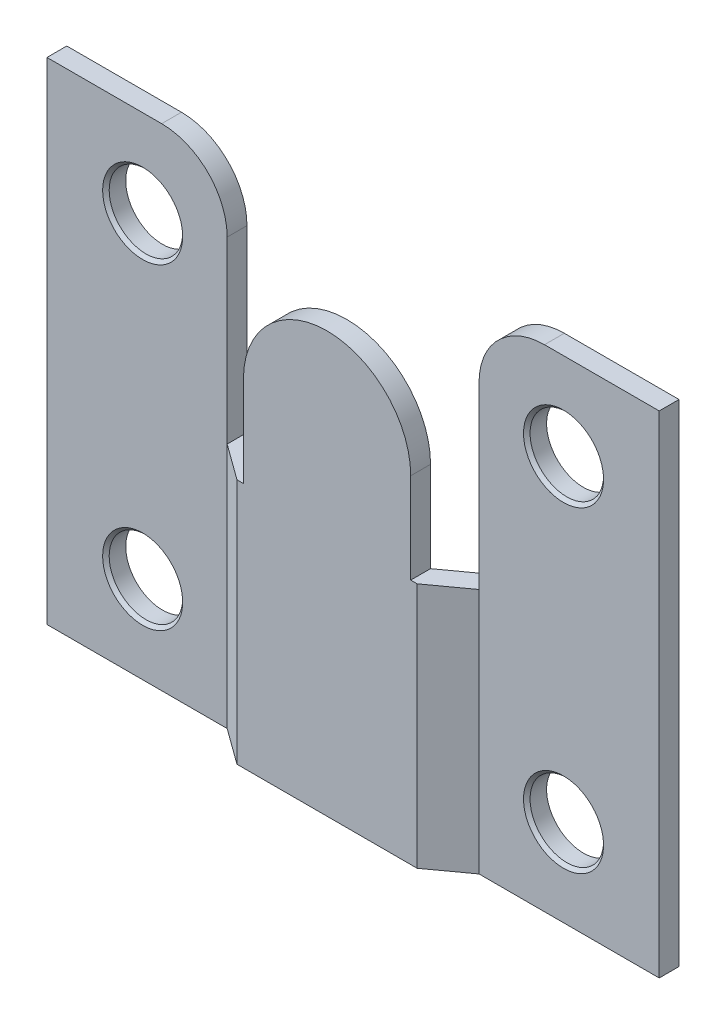
SolidWorks part; units mm, degrees
ref_plane "Front" through (0, 0, 0) normal (0, 0, 1) x (1, 0, 0)
ref_plane "Top" through (0, 0, 0) normal (0, 1, 0) x (1, 0, 0)
ref_plane "Right" through (0, 0, 0) normal (1, 0, 0) x (0, 0, -1)
sketch "Sketch1" plane through (0, 0, 0) normal (0, 1, 0) x (1, 0, 0)
  line L0 (9.7701, 2.0193) -> (6.9894, 0)
  line L1 (6.9894, 0) -> (-6.9894, 0)
  line L2 (-6.9894, 0) -> (-9.7701, 2.0193)
  line L3 (-9.7701, 2.0193) -> (-23.749, 2.0193)
  line L4 (9.7701, 2.0193) -> (23.749, 2.0193)
  line L5 (0, 0) -> (0, 3.556) construction
  line L6 (9.271, 3.556) -> (23.749, 3.556)
  line L7 (9.271, 3.556) -> (6.4903, 1.5367)
  line L8 (6.4903, 1.5367) -> (-6.4903, 1.5367)
  line L9 (-6.4903, 1.5367) -> (-9.271, 3.556)
  line L10 (-9.271, 3.556) -> (-23.749, 3.556)
  line L12 (-23.749, 3.556) -> (-23.749, 2.0193)
  line L13 (23.749, 3.556) -> (23.749, 2.0193)
  point P15 (0, 0)
  dimension "D1" = 47.498
  dimension "D2" = 3.556
  dimension "D3" = 14.478
  dimension "D4" = 1.5367
extrude "Boss-Extrude1" add sketch "Sketch1" along normal blind 38.1
sketch "Sketch2" plane through (0, 0, 0) normal (0, 0, 1) x (1, 0, 0)
  line L0 (-23.749, 19.05) -> (23.749, 19.05) construction
  line L1 (-23.749, 38.1) -> (-23.749, 0) construction
  line L2 (23.749, 38.1) -> (23.749, 0) construction
  line L3 (-9.7701, 38.1) -> (-9.7701, 0) construction
  line L4 (-9.7701, 19.05) -> (-6.9894, 19.05)
  line L5 (-9.7701, 19.05) -> (-9.7701, 38.1)
  line L6 (-9.7701, 38.1) -> (-6.9894, 38.1)
  line L7 (-6.9894, 19.05) -> (-6.9894, 38.1)
  line L8 (6.9894, 38.1) -> (6.9894, 0) construction
  line L9 (6.9894, 19.05) -> (9.7701, 19.05)
  line L10 (6.9894, 19.05) -> (6.9894, 38.1)
  line L11 (6.9894, 38.1) -> (9.7701, 38.1)
  line L12 (9.7701, 19.05) -> (9.7701, 38.1)
sketch "Sketch5" plane through (0, 0, -2.0193) normal (0, 0, 1) x (1, 0, 0)
  line L0 (-9.7701, 0) -> (-9.7701, 19.1135) construction
  line L1 (-9.7701, 38.1) -> (-9.7701, 0) construction
  dimension "D1" = 19.1135
sketch "Sketch3" plane through (0, 38.1, 0) normal (0, 1, 0) x (1, 0, 0)
  line L0 (-9.7701, 3.9185) -> (-9.7701, 2.0193)
  line L1 (-9.7701, 2.0193) -> (-6.4903, -0.3625)
  line L2 (-6.4903, 1.5367) -> (-6.4903, -0.3625)
  line L3 (-6.4903, 1.5367) -> (-9.271, 3.556) construction
  line L4 (-6.4903, 1.5367) -> (-9.7701, 3.9185)
  line L5 (0, 0) -> (0, 2.8575) construction
  line L6 (-6.9894, 0) -> (6.9894, 0) construction
  line L7 (-9.7701, 2.0193) -> (-6.9894, 0) construction
  line L8 (6.4903, 1.5367) -> (9.7701, 3.9185)
  line L9 (6.4903, 1.5367) -> (6.4903, -0.3625)
  line L10 (9.7701, 2.0193) -> (6.4903, -0.3625)
  line L11 (9.7701, 3.9185) -> (9.7701, 2.0193)
extrude "Cut-Extrude2" cut sketch "Sketch3" against normal up to vertex (18.9865 mm away) up to point (-9.7701, 19.1135, -2.0193)
sketch "Sketch6" plane through (0, 0, -1.5367) normal (0, 0, -1) x (-1, 0, 0)
  line L0 (-6.4903, 38.1) -> (-6.4903, 19.1135) construction
  line L1 (6.4903, 38.1) -> (6.4903, 19.1135) construction
  line L2 (0, 32.6136) -> (0, 38.1) construction
  line L3 (-6.4903, 38.1) -> (6.4903, 38.1) construction
  line L4 (0, 32.6136) -> (0, 19.05) construction
  line L5 (23.749, 19.05) -> (-23.749, 19.05) construction
  line L6 (-6.4903, 26.1233) -> (-8.4085, 26.1233)
  line L7 (-8.4085, 26.1233) -> (-8.4085, 40.6251)
  line L8 (-8.4085, 40.6251) -> (8.3135, 40.6251)
  line L9 (8.3135, 40.6251) -> (8.3135, 26.1233)
  line L10 (8.3135, 26.1233) -> (6.4903, 26.1233)
  arc A0 (-6.4903, 26.1233) -> (6.4903, 26.1233) centre (0, 26.1233) cw
  dimension "D1" = 13.5636
  dimension "D2" = 16.7219
  dimension "D3" = 14.5018
  dimension "D4" = 1.9181
extrude "Cut-Extrude4" cut sketch "Sketch6" against normal through all both and the other way through all
fillet "Fillet3" radius 5.08 2 edges at (9.7701, 38.1, -2.7877) (-9.7701, 38.1, -2.7877)
sketch "Sketch7" plane through (0, 0, -2.0193) normal (0, 0, 1) x (1, 0, 0)
  line L0 (-23.749, 19.05) -> (23.749, 19.05) construction
  line L1 (-16.3259, 31.3373) -> (16.3258, 31.3373) construction
  line L2 (-16.3259, 31.3373) -> (-16.3259, 6.7628) construction
  line L3 (-16.3259, 6.7628) -> (16.3258, 6.7628) construction
  line L4 (16.3258, 31.3373) -> (16.3258, 6.7628) construction
  line L5 (-16.3259, 31.3373) -> (16.3258, 6.7628) construction
  line L6 (-16.3259, 6.7628) -> (16.3258, 31.3373) construction
  circle A0 centre (-16.3259, 31.3373) radius 2.8512 construction
  circle A1 centre (16.3258, 31.3373) radius 2.8512 construction
  circle A2 centre (16.3258, 6.7628) radius 2.8511 construction
  circle A3 centre (-16.3259, 6.7628) radius 2.8511 construction
  point P0 (0, 19.05)
  point P9 (-19.177, 31.3373)
  point P10 (19.177, 31.3373)
  point P11 (-16.3259, 3.9116)
  point P12 (-16.3259, 34.1884)
  dimension "D1" = 5.7023
  dimension "D2" = 38.354
  dimension "D3" = 30.2768
sketch "Sketch8" plane through (0, 0, -2.0193) normal (0, 0, 1) x (1, 0, 0)
  circle A0 centre (-16.3259, 31.3373) radius 2.8512 construction
  circle A1 centre (-16.3259, 6.7628) radius 2.8512 construction
  circle A2 centre (16.3258, 6.7628) radius 2.8512 construction
  circle A3 centre (16.3258, 31.3373) radius 2.8512 construction
  circle A4 centre (-16.3259, 31.3373) radius 2.8512
  circle A5 centre (-16.3259, 6.7628) radius 2.8511
  circle A6 centre (16.3258, 6.7628) radius 2.8511
  circle A7 centre (16.3258, 31.3373) radius 2.8512
extrude "Cut-Extrude5" cut sketch "Sketch8" against normal through all both and the other way through all
chamfer "Chamfer1" distance 0.254 angle 45 4 edges at (13.4747, 6.7628, -2.0193) (-19.177, 6.7628, -2.0193) (13.4747, 31.3373, -2.0193) (-19.177, 31.3373, -2.0193)
